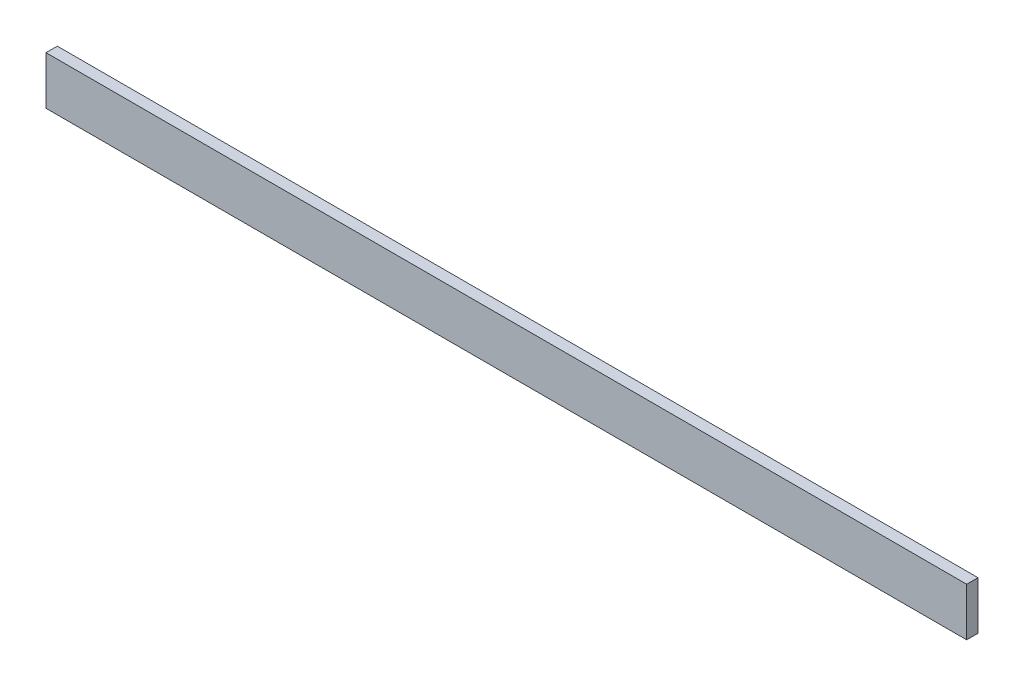
SolidWorks part; units mm, degrees
ref_plane "Front Plane" through (0, 0, 0) normal (0, 0, 1) x (1, 0, 0)
ref_plane "Top Plane" through (0, 0, 0) normal (0, 1, 0) x (1, 0, 0)
ref_plane "Right Plane" through (0, 0, 0) normal (1, 0, 0) x (0, 0, -1)
sketch "Sketch1" plane through (0, 0, 0) normal (0, 0, 1) x (1, 0, 0)
  line L1 (-485.394, -25.4) -> (485.394, -25.4)
  line L2 (-485.394, -25.4) -> (-485.394, 25.4)
  line L3 (-485.394, 25.4) -> (485.394, 25.4)
  line L4 (485.394, -25.4) -> (485.394, 25.4)
  line L5 (-485.394, -25.4) -> (485.394, 25.4) construction
  line L6 (-485.394, 25.4) -> (485.394, -25.4) construction
  point P0 (0, 0)
  dimension "D1" = 50.8
  dimension "D2" = 970.788
extrude "Boss-Extrude1" add sketch "Sketch1" along normal blind 11.938
